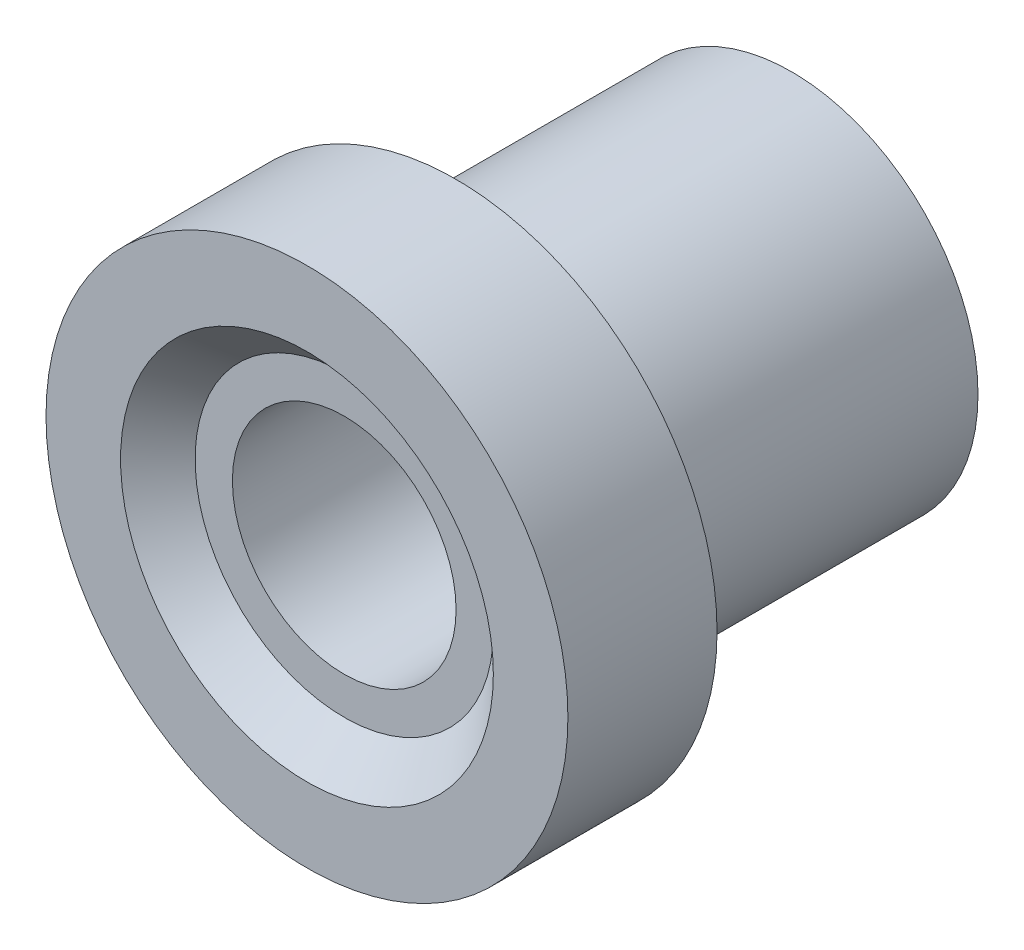
SolidWorks part; units mm, degrees
material "AISI 1020"
ref_plane "Спереди" through (0, 0, 0) normal (0, 0, 1) x (1, 0, 0)
ref_plane "Сверху" through (0, 0, 0) normal (0, 1, 0) x (1, 0, 0)
ref_plane "Справа" through (0, 0, 0) normal (1, 0, 0) x (0, 0, -1)
sketch "Эскиз1" plane through (0, 0, 0) normal (1, 0, 0) x (0, 0, -1)
  line L0 (-4, 7) -> (-4, 5) construction
  line L1 (-4, 5) -> (-3, 4) construction
  line L2 (-3, 4) -> (-3, 3) construction
  line L4 (0, 7) -> (0, 3) construction
  line L5 (0, 7) -> (-4, 7) construction
  line L6 (-4, 7) -> (-4, 5)
  line L7 (-4, 5) -> (-3, 4)
  line L8 (-3, 4) -> (-3, 3)
  line L9 (9, 2.9981) -> (-3, 3)
  line L10 (0, 7) -> (0, 5)
  line L11 (0, 7) -> (-4, 7)
  line L12 (-1000, 0) -> (49000, 0) construction
  line L13 (0, 5) -> (9, 5)
  line L14 (9, 5) -> (9, 2.9981)
  line L15 (9, -11.5) -> (9, 11.5) construction
  line L16 (24.25, 2.9981) -> (-3, 2.9981) construction
revolve "Повернуть1" add sketch "Эскиз1" angle 360 about L12
